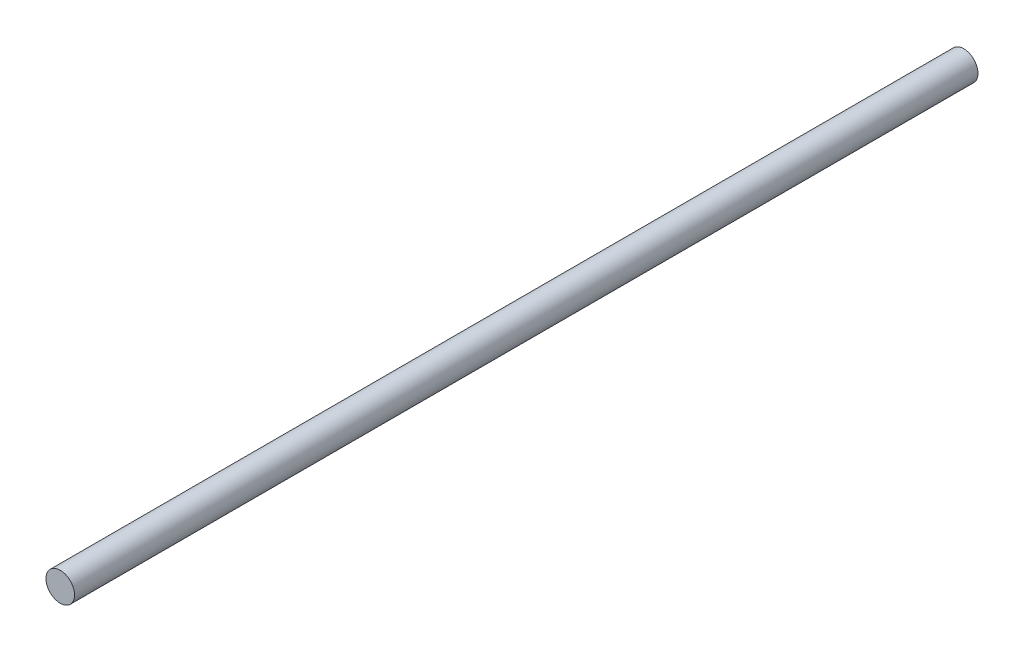
SolidWorks part; units mm, degrees
ref_plane "Front Plane" through (0, 0, 0) normal (0, 0, 1) x (1, 0, 0)
ref_plane "Top Plane" through (0, 0, 0) normal (0, 1, 0) x (1, 0, 0)
ref_plane "Right Plane" through (0, 0, 0) normal (1, 0, 0) x (0, 0, -1)
sketch "Sketch1" plane through (0, 0, 0) normal (0, 0, 1) x (1, 0, 0)
  circle A0 centre (-10.0166, -10.0166) radius 3.7971 construction
  circle A1 centre (-10.0166, -10.0166) radius 3.7971
extrude "Boss-Extrude1" add sketch "Sketch1" along normal up to surface (240 mm away)
